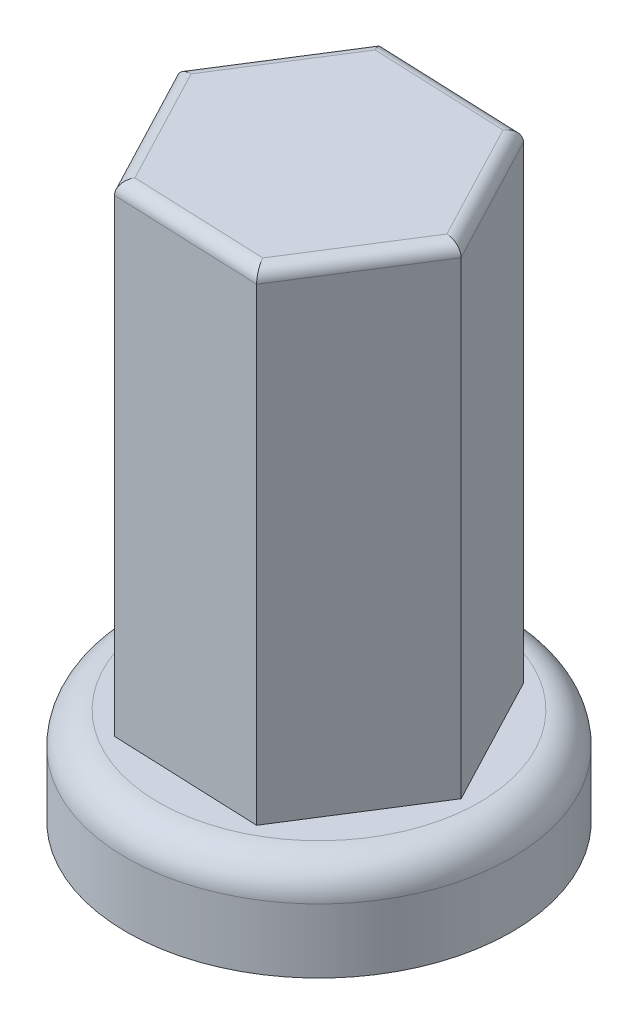
SolidWorks part; units mm, degrees
ref_plane "Front Plane" through (0, 0, 0) normal (0, 0, 1) x (1, 0, 0)
ref_plane "Top Plane" through (0, 0, 0) normal (0, 1, 0) x (1, 0, 0)
ref_plane "Right Plane" through (0, 0, 0) normal (1, 0, 0) x (0, 0, -1)
sketch "Sketch1" plane through (0, 0, 0) normal (0, 1, 0) x (1, 0, 0)
  circle A0 centre (0, 0) radius 7.62
  dimension "D1" = 15.24
extrude "Boss-Extrude1" add sketch "Sketch1" along normal blind 3.81
sketch "Sketch2" plane through (0, 3.81, 0) normal (0, 1, 0) x (1, 0, 0)
  line L1 (5.8611, -0.2369) -> (3.1357, 4.9574)
  line L2 (3.1357, 4.9574) -> (-2.7254, 5.1943)
  line L3 (-2.7254, 5.1943) -> (-5.8611, 0.2369)
  line L4 (-5.8611, 0.2369) -> (-3.1357, -4.9574)
  line L5 (-3.1357, -4.9574) -> (2.7254, -5.1943)
  line L6 (2.7254, -5.1943) -> (5.8611, -0.2369)
  circle A0 centre (0, 0) radius 5.08 construction
  dimension "D1" = 10.16
extrude "Boss-Extrude2" add sketch "Sketch2" along normal blind 19.05
fillet "Fillet1" radius 1.27 1 edges at (0, 3.81, 7.62)
fillet "Fillet2" radius 0.508 6 edges at (-4.4984, 22.86, 2.3603) (-4.2932, 22.86, -2.7156) (0.2051, 22.86, -5.0759) (4.4984, 22.86, -2.3603) (4.2932, 22.86, 2.7156) (-0.2051, 22.86, 5.0759)
sketch "Sketch3" plane through (0, 0, 0) normal (0, -1, 0) x (1, 0, 0)
  circle A0 centre (0, 0) radius 4.699
  dimension "D1" = 9.398
extrude "Cut-Extrude1" cut sketch "Sketch3" against normal blind 19.05
